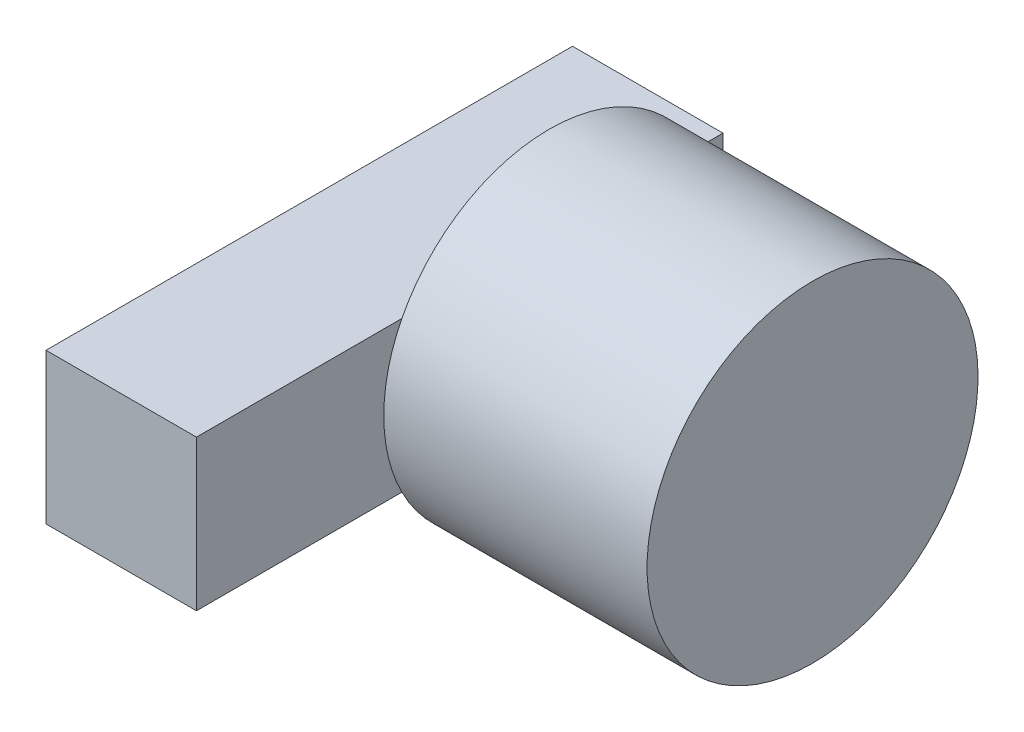
SolidWorks part; units mm, degrees
ref_plane "Ebene vorne" through (0, 0, 0) normal (0, 0, 1) x (1, 0, 0)
ref_plane "Ebene oben" through (0, 0, 0) normal (0, 1, 0) x (1, 0, 0)
ref_plane "Ebene rechts" through (0, 0, 0) normal (1, 0, 0) x (0, 0, -1)
sketch "Skizze3" plane through (0, 0, 0) normal (0, 0, 1) x (1, 0, 0)
  line L1 (10, 10) -> (-10, 10)
  line L2 (10, 10) -> (10, -10)
  line L3 (10, -10) -> (-10, -10)
  line L4 (-10, 10) -> (-10, -10)
  line L5 (10, 10) -> (-10, -10) construction
  line L6 (10, -10) -> (-10, 10) construction
  point P0 (0, 0)
  dimension "D1" = 20
  dimension "D2" = 20
extrude "Aufsatz-Linear austragen2" add sketch "Skizze3" along normal blind 70
sketch "Skizze4" plane through (10, 0, 0) normal (1, 0, 0) x (0, 0, -1)
  circle A0 centre (-23.0922, 0) radius 22
  dimension "D1" = 44
extrude "Aufsatz-Linear austragen3" add sketch "Skizze4" along normal blind 35
